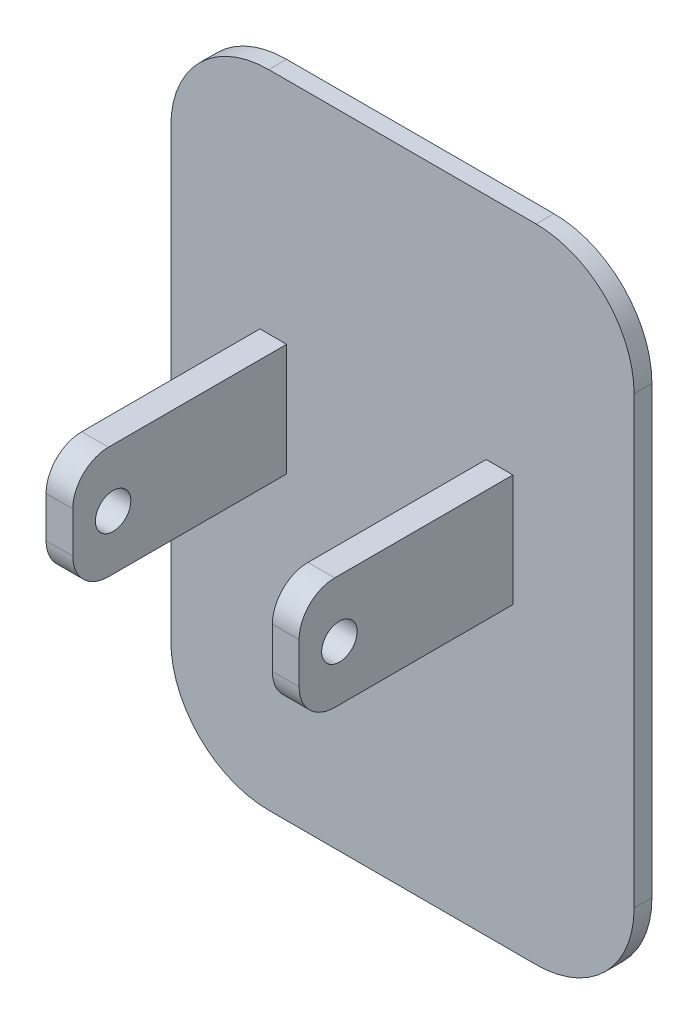
SolidWorks part; units mm, degrees
ref_plane "Front Plane" through (0, 0, 0) normal (0, 0, 1) x (1, 0, 0)
ref_plane "Top Plane" through (0, 0, 0) normal (0, 1, 0) x (1, 0, 0)
ref_plane "Right Plane" through (0, 0, 0) normal (1, 0, 0) x (0, 0, -1)
sketch "Sketch1" plane through (0, 0, 0) normal (0, 0, 1) x (1, 0, 0)
  line L0 (13.9, -10.6375) -> (13.9, 14.3625)
  line L1 (-6.6, -16.1375) -> (8.4, -16.1375)
  line L2 (-12.1, 14.3625) -> (-12.1, -10.6375)
  line L3 (8.4, 19.8625) -> (-6.6, 19.8625)
  line L5 (-7.1, 7.0135) -> (-5.6, 7.0135)
  line L6 (-7.1, 7.0135) -> (-7.1, 0.7135)
  line L7 (-7.1, 0.7135) -> (-5.6, 0.7135)
  line L8 (-5.6, 7.0135) -> (-5.6, 0.7135)
  line L9 (-7.1, 7.0135) -> (-5.6, 0.7135) construction
  line L10 (-7.1, 0.7135) -> (-5.6, 7.0135) construction
  line L11 (5.6, 0.7135) -> (7.1, 0.7135)
  line L12 (5.6, 0.7135) -> (5.6, 7.0135)
  line L13 (5.6, 7.0135) -> (7.1, 7.0135)
  line L14 (7.1, 0.7135) -> (7.1, 7.0135)
  line L15 (5.6, 0.7135) -> (7.1, 7.0135) construction
  line L16 (5.6, 7.0135) -> (7.1, 0.7135) construction
  arc A0 (8.4, -16.1375) -> (13.9, -10.6375) centre (8.4, -10.6375) ccw
  arc A1 (-12.1, -10.6375) -> (-6.6, -16.1375) centre (-6.6, -10.6375) ccw
  arc A2 (-6.6, 19.8625) -> (-12.1, 14.3625) centre (-6.6, 14.3625) ccw
  arc A3 (13.9, 14.3625) -> (8.4, 19.8625) centre (8.4, 14.3625) ccw
  point P16 (-6.35, 3.8635)
  point P21 (6.35, 3.8635)
  point P22 (6.35, 0.7135)
  point P23 (-6.35, 0.7135)
  dimension "D1" = 26
  dimension "D2" = 36
  dimension "D3" = 1.5
  dimension "D4" = 1.5
  dimension "D5" = 6.3
  dimension "D6" = 6.3
  dimension "D7" = 12.7
  dimension "D8" = 5
extrude "Boss-Extrude1" add sketch "Sketch1" along normal blind 1
sketch "Sketch2" plane through (0, 0, 1) normal (0, 0, 1) x (1, 0, 0)
  line L1 (-7.1, 0.7135) -> (-5.6, 0.7135)
  line L2 (-7.1, 0.7135) -> (-7.1, 7.0135)
  line L3 (-7.1, 7.0135) -> (-5.6, 7.0135)
  line L4 (-5.6, 0.7135) -> (-5.6, 7.0135)
  line L5 (5.6, 0.7135) -> (7.1, 0.7135)
  line L6 (5.6, 0.7135) -> (5.6, 7.0135)
  line L7 (5.6, 7.0135) -> (7.1, 7.0135)
  line L8 (7.1, 0.7135) -> (7.1, 7.0135)
extrude "Boss-Extrude2" add sketch "Sketch2" along normal blind 12 separate body
sketch "Sketch3" plane through (7.1, 0, 0) normal (1, 0, 0) x (0, 0, -1)
  circle A0 centre (-10.7396, 3.781) radius 0.9948
extrude "Cut-Extrude1" cut sketch "Sketch3" against normal through all
fillet "Fillet1" radius 2 2 edges at (6.35, 7.0135, 13) (6.35, 0.7135, 13)
fillet "Fillet2" radius 2 2 edges at (-6.35, 7.0135, 13) (-6.35, 0.7135, 13)
